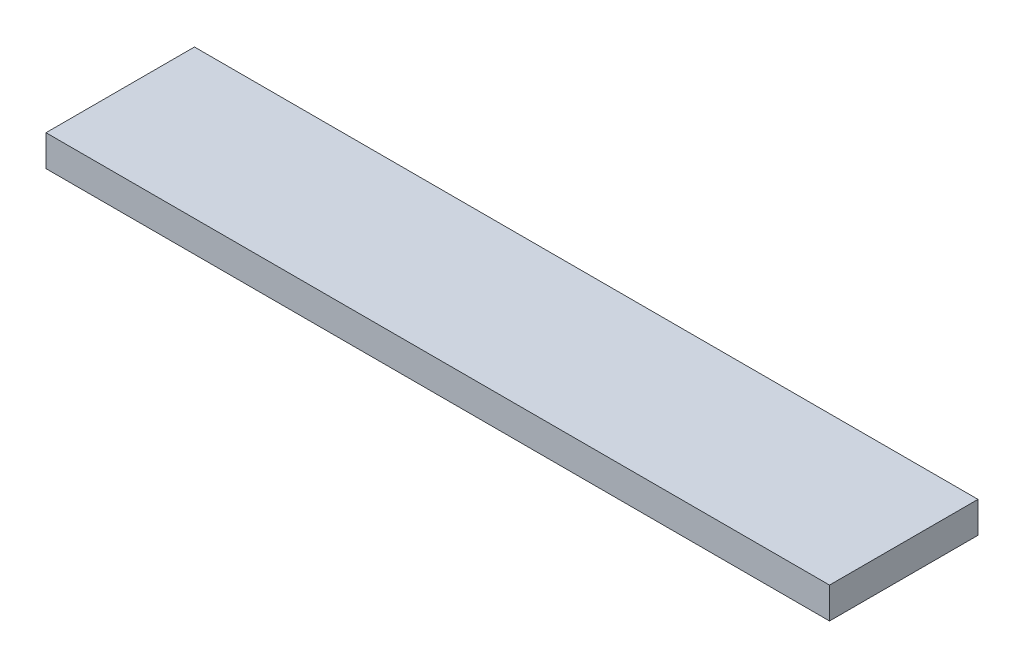
SolidWorks part; units mm, degrees
material "Oak"
ref_plane "Front Plane" through (0, 0, 0) normal (0, 0, 1) x (1, 0, 0)
ref_plane "Top Plane" through (0, 0, 0) normal (0, 1, 0) x (1, 0, 0)
ref_plane "Right Plane" through (0, 0, 0) normal (1, 0, 0) x (0, 0, -1)
sketch "Sketch1" plane through (0, 0, 0) normal (0, 1, 0) x (1, 0, 0)
  line L1 (0, 0) -> (479.3488, 0)
  line L2 (0, 0) -> (0, 90.8304)
  line L3 (0, 90.8304) -> (479.3488, 90.8304)
  line L4 (479.3488, 0) -> (479.3488, 90.8304)
  dimension "D1" = 90.8304
  dimension "D2" = 479.3488
extrude "Boss-Extrude1" add sketch "Sketch1" along normal blind 19.05
